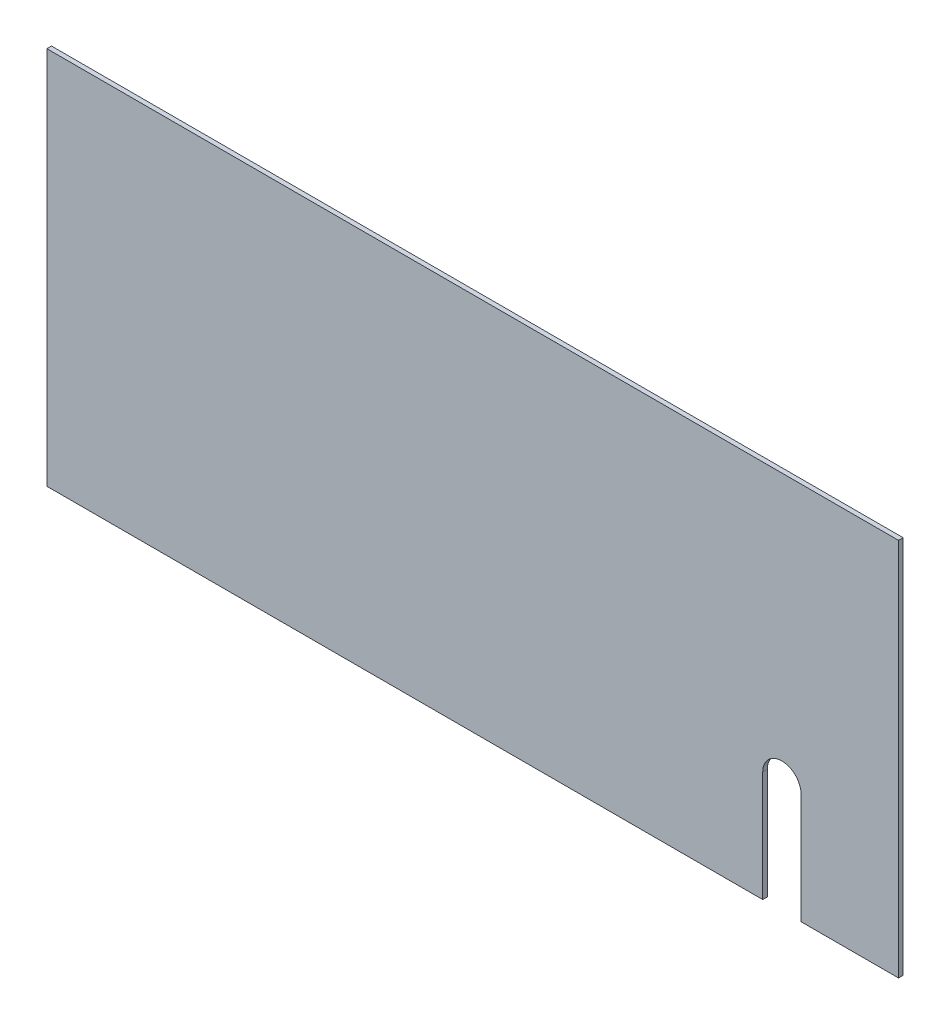
SolidWorks part; units mm, degrees
ref_plane "Plan de face" through (0, 0, 0) normal (0, 0, 1) x (1, 0, 0)
ref_plane "Plan de dessus" through (0, 0, 0) normal (0, 1, 0) x (1, 0, 0)
ref_plane "Plan de droite" through (0, 0, 0) normal (1, 0, 0) x (0, 0, -1)
sketch "Esquisse1" plane through (0, 0, 0) normal (0, 0, 1) x (1, 0, 0)
  line L1 (267.2567, -2.1662) -> (-287.7433, -2.1662)
  line L2 (267.2567, -2.1662) -> (267.2567, 244.8338)
  line L3 (267.2567, 244.8338) -> (-287.7433, 244.8338)
  line L4 (-287.7433, -2.1662) -> (-287.7433, 244.8338)
  dimension "D1" = 555
extrude "Boss.-Extru.1" add sketch "Esquisse1" along normal blind 3
sketch "Esquisse3" plane through (0, 0, 3) normal (0, 0, 1) x (1, 0, 0)
  line L0 (-287.7433, -2.1662) -> (267.2567, -2.1662) construction
  line L1 (-132.7433, 183.8338) -> (67.2567, 183.8338) construction
  line L2 (-132.7433, 183.8338) -> (-132.7433, 87.8338) construction
  line L3 (-132.7433, 87.8338) -> (67.2567, 87.8338) construction
  line L4 (67.2567, 183.8338) -> (67.2567, 87.8338) construction
  line L5 (-287.7433, -2.1662) -> (267.2567, -2.1662) construction
  line L6 (267.2567, -2.1662) -> (267.2567, 244.8338) construction
  line L7 (178.7567, 69.8338) -> (178.7567, -2.1662)
  line L8 (-287.7433, -2.1662) -> (267.2567, -2.1662) construction
  line L9 (267.2567, -2.1662) -> (267.2567, 244.8338) construction
  line L10 (178.7567, -2.1662) -> (203.7567, -2.1662)
  line L11 (203.7567, -2.1662) -> (203.7567, 69.8338)
  circle A0 centre (-132.7433, 183.8338) radius 6.5 construction
  circle A1 centre (-132.7433, 87.8338) radius 6.5 construction
  circle A2 centre (67.2567, 87.8338) radius 6.5 construction
  circle A3 centre (67.2567, 183.8338) radius 6.5 construction
  arc A4 (203.7567, 69.8338) -> (178.7567, 69.8338) centre (191.2567, 69.8338) ccw
  dimension "D1" = 13
  dimension "D6" = 25
  dimension "D7" = 72
  dimension "D8" = 76
  dimension "D2" = 96
  dimension "D3" = 200
  dimension "D4" = 90
  dimension "D5" = 200
extrude "Enlèv. mat.-Extru.2" cut sketch "Esquisse3" against normal blind 72
sketch "Esquisse5" plane through (0, 0, 3) normal (0, 0, 1) x (1, 0, 0)
  arc A0 (195.0515, 92.9592) -> (167.882, 68.1584) centre (191.2567, 69.8338) ccw construction
  text T0 "Direction" font "Century Gothic" height in points 72
